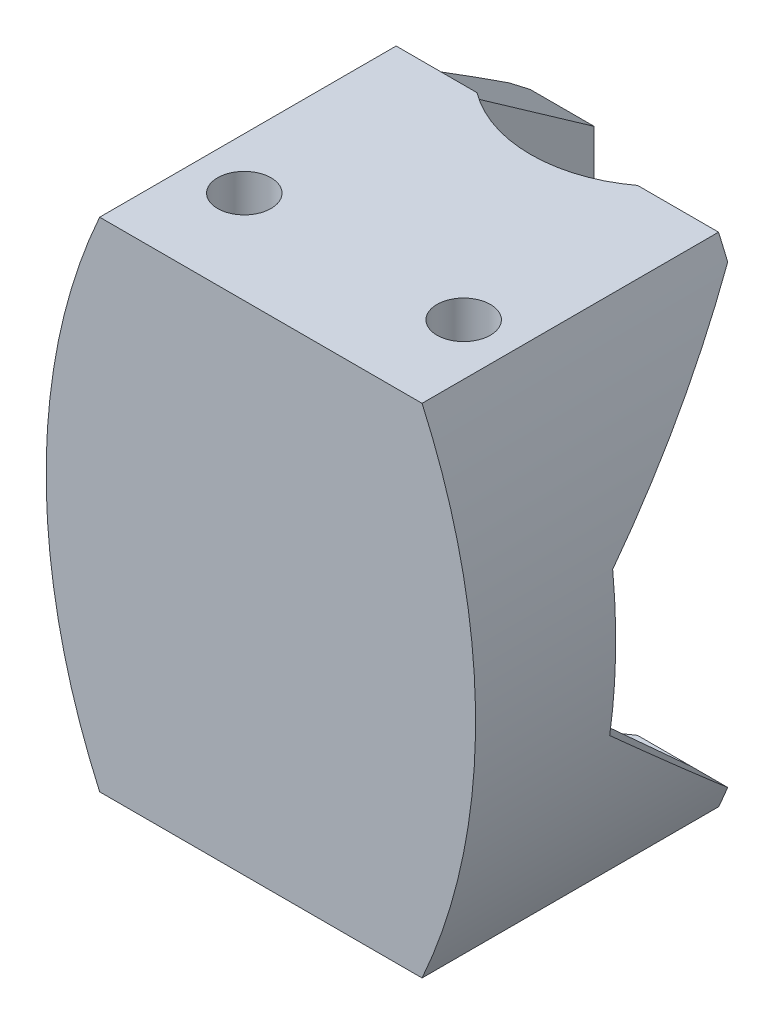
SolidWorks part; units mm, degrees
ref_plane "Front Plane" through (0, 0, 0) normal (0, 0, 1) x (1, 0, 0)
ref_plane "Top Plane" through (0, 0, 0) normal (0, 1, 0) x (1, 0, 0)
ref_plane "Right Plane" through (0, 0, 0) normal (1, 0, 0) x (0, 0, -1)
sketch "Sketch2" plane through (0, 0, 0) normal (0, 1, 0) x (1, 0, 0)
  line L0 (15.061, 0) -> (15.061, 37.7)
  line L1 (-12.561, 2.5) -> (12.561, 2.5)
  line L2 (-12.561, 2.5) -> (-12.561, 37.7)
  line L4 (12.561, 2.5) -> (12.561, 37.7)
  line L5 (15.061, 37.7) -> (12.561, 37.7)
  line L7 (-15.061, 37.7) -> (-15.061, 0)
  line L8 (-15.061, 0) -> (15.061, 0)
  line L10 (-15.061, 37.7) -> (-12.561, 37.7)
  point P4 (0, 2.5)
  point P12 (0, 0)
  dimension "D1" = 2.5
  dimension "D2" = 2.5
  dimension "D3" = 37.7
  dimension "D4" = 25.122
  dimension "D5" = 15.061
extrude "Boss-Extrude1" add sketch "Sketch2" along normal blind 32.5
sketch "Sketch4" plane through (0, 0, 0) normal (0, -1, 0) x (1, 0, 0)
  line L0 (-15.061, 0) -> (-15.061, -7.4438)
  line L8 (15.061, -7.4438) -> (15.061, 0)
  line L9 (15.061, 0) -> (-15.061, 0)
  line L10 (15.061, 0) -> (15.061, -37.7) construction
  line L13 (-15.061, -7.4438) -> (-15.061, -37.7)
  line L23 (-15.061, -37.7) -> (-12.561, -37.7)
  line L34 (-12.561, -37.7) -> (-12.561, -7.5)
  line L35 (-12.561, -2.5) -> (-12.561, -37.7) construction
  line L36 (-12.561, -7.5) -> (12.561, -7.5)
  line L37 (12.561, -37.7) -> (12.561, -2.5) construction
  line L38 (12.561, -7.5) -> (12.561, -37.7)
  line L39 (12.561, -37.7) -> (15.061, -37.7)
  line L40 (15.061, -37.7) -> (15.061, -7.4438)
  circle A2 centre (-10.2499, -4.95) radius 1.05
  circle A5 centre (10.2499, -4.95) radius 1.05
  dimension "D5" = 2.1
  dimension "D1" = 7.5
  dimension "D6" = 4.8111
  dimension "D7" = 4.95
  dimension "D8" = 4.8111
extrude "Boss-Extrude2" add sketch "Sketch4" along normal blind 2
sketch "Sketch7" plane through (0, -2, 0) normal (0, -1, 0) x (1, 0, 0)
  line L0 (-15.061, 0) -> (-15.061, -37.7)
  line L1 (-15.061, -37.7) -> (-12.561, -37.7)
  line L2 (-15.061, 0) -> (15.061, 0)
  line L4 (15.061, 0) -> (15.061, -37.7)
  line L5 (15.061, -37.7) -> (12.561, -37.7)
  line L6 (12.561, -37.7) -> (12.561, -7.5)
  line L7 (12.561, -7.5) -> (-12.561, -7.5)
  line L8 (-12.561, -7.5) -> (-12.561, -37.7)
  circle A2 centre (-10.2499, -4.95) radius 2.495
  circle A3 centre (10.2499, -4.95) radius 2.495
  dimension "D1" = 4.99
extrude "Wire spacing2" add sketch "Sketch7" along normal blind 3
sketch "Sketch8" plane through (0, -5, 0) normal (0, -1, 0) x (1, 0, 0)
  line L0 (-15.061, 0) -> (-15.061, -37.7)
  line L1 (-15.061, -37.7) -> (15.061, -37.7)
  line L2 (15.061, -37.7) -> (15.061, 0) construction
  line L3 (12.561, -37.7) -> (15.061, -37.7) construction
  line L4 (-15.061, 0) -> (15.061, 0)
  line L6 (15.061, 0) -> (15.061, -37.7)
  circle A0 centre (-10.2499, -4.95) radius 2.495
  circle A1 centre (10.2499, -4.95) radius 2.495
  circle A2 centre (10.2499, -4.95) radius 2.495 construction
  circle A3 centre (-10.2499, -4.95) radius 2.495 construction
extrude "Boss-Extrude6" add sketch "Sketch8" along normal blind 2
sketch "Sketch5" plane through (0, 32.5, 0) normal (0, 1, 0) x (1, 0, 0)
  line L0 (-7.5, 10) -> (-7.5, 2.5)
  line L9 (12.561, 2.5) -> (-12.561, 2.5) construction
  line L11 (-10.2499, 12) -> (-7.5, 10)
  line L13 (-15.061, 0) -> (15.061, 0) construction
  line L15 (-15.061, 0) -> (-15.061, 37.7)
  line L17 (10.2499, 12) -> (7.5, 10)
  line L20 (15.061, 0) -> (15.061, 37.7)
  line L21 (-7.5, 2.5) -> (7.5, 2.5)
  line L22 (7.5, 2.5) -> (7.5, 10)
  line L23 (-15.061, 0) -> (15.061, 0)
  line L24 (-10.2499, 12) -> (-12.561, 12)
  line L25 (-12.561, 37.7) -> (-12.561, 7.5) construction
  line L26 (-12.561, 12) -> (-12.561, 37.7)
  line L27 (-12.561, 37.7) -> (-15.061, 37.7)
  line L30 (15.061, 37.7) -> (12.561, 37.7)
  line L31 (12.561, 37.7) -> (12.561, 12)
  line L32 (12.561, 7.5) -> (12.561, 37.7) construction
  line L33 (12.561, 12) -> (10.2499, 12)
  circle A0 centre (-10.2499, 4.95) radius 1.05 construction
  circle A1 centre (-10.2499, 8.7) radius 1.05
  circle A2 centre (10.2499, 8.7) radius 1.05
  dimension "D4" = 0
  dimension "D7" = 8.7
  dimension "D1" = 12
  dimension "D2" = 7.561
  dimension "D3" = 20.4998
  dimension "D5" = 10
  dimension "D6" = 7.561
extrude "Boss-Extrude3" add sketch "Sketch5" along normal blind 2
sketch "Sketch9" plane through (0, 34.5, 0) normal (0, 1, 0) x (1, 0, 0)
  line L0 (-15.061, 0) -> (-15.061, 37.7)
  line L1 (-15.061, 37.7) -> (-12.561, 37.7)
  line L2 (-12.561, 37.7) -> (-12.561, 12)
  line L3 (-12.561, 12) -> (-10.2499, 12)
  line L4 (-10.2499, 12) -> (-7.5, 10)
  line L5 (-7.5, 10) -> (-7.5, 2.5)
  line L6 (-7.5, 2.5) -> (7.5, 2.5)
  line L7 (7.5, 2.5) -> (7.5, 10)
  line L8 (7.5, 10) -> (10.2499, 12)
  line L9 (10.2499, 12) -> (7.5, 10) construction
  line L10 (10.2499, 12) -> (12.561, 12)
  line L11 (12.561, 7.5) -> (12.561, 37.7) construction
  line L12 (12.561, 12) -> (12.561, 37.7)
  line L13 (12.561, 37.7) -> (15.061, 37.7)
  line L14 (15.061, 0) -> (15.061, 37.7) construction
  line L15 (15.061, 37.7) -> (12.561, 37.7) construction
  line L16 (15.061, 37.7) -> (15.061, 0)
  line L17 (15.061, 0) -> (-15.061, 0)
  circle A0 centre (-10.2499, 8.7) radius 2.495
  circle A1 centre (10.2499, 8.7) radius 2.495
  dimension "D1" = 4.99
extrude "Wire spacing1" add sketch "Sketch9" along normal blind 3
sketch "Sketch10" plane through (0, 37.5, 0) normal (0, 1, 0) x (1, 0, 0)
  line L1 (-15.061, 37.7) -> (15.061, 37.7)
  line L2 (-15.061, 37.7) -> (-15.061, 0)
  line L3 (-15.061, 0) -> (15.061, 0)
  line L4 (15.061, 37.7) -> (15.061, 0)
  circle A0 centre (-10.2499, 8.7) radius 2.495
  circle A1 centre (10.2499, 8.7) radius 2.495
  circle A2 centre (-10.2499, 8.7) radius 2.495 construction
  circle A3 centre (10.2499, 8.7) radius 2.495 construction
extrude "Boss-Extrude8" add sketch "Sketch10" along normal blind 2
sketch "Sketch11" plane through (0, 39.5, 0) normal (0, 1, 0) x (1, 0, 0)
  line L0 (15.061, 37.7) -> (-15.061, 37.7) construction
  circle A0 centre (0, 37.7) radius 12.5
  dimension "D1" = 25
extrude "Cut-Extrude1" cut sketch "Sketch11" against normal through all
ref_plane "Box Mid Plane" through (0, 16.25, 0) normal (0, 1, 0) x (1, 0, 0)
sketch "Sketch18" plane through (0, 39.5, 0) normal (0, 1, 0) x (1, 0, 0)
  line L1 (-15.061, 37.7) -> (-5.061, 37.7)
  line L2 (-15.061, 37.7) -> (-15.061, 27.7)
  line L3 (-15.061, 27.7) -> (-5.061, 27.7)
  line L4 (-5.061, 37.7) -> (-5.061, 27.7)
  line L5 (15.061, 37.7) -> (5.061, 37.7)
  line L6 (15.061, 37.7) -> (15.061, 27.7)
  line L7 (15.061, 27.7) -> (5.061, 27.7)
  line L8 (5.061, 37.7) -> (5.061, 27.7)
  dimension "D1" = 10
  dimension "D2" = 10
extrude "Cut-Extrude4" cut sketch "Sketch18" against normal through all
sketch "Sketch19" plane through (-15.061, 0, 0) normal (-1, 0, 0) x (0, 0, 1)
  line L0 (-27.7, 37.5) -> (-43.7, 26.25)
  line L1 (-43.7, 26.25) -> (-43.7, 6.25)
  line L2 (-43.7, 6.25) -> (-27.7, -5)
  line L3 (-27.7, -5) -> (-27.7, 37.5)
  point P3 (-27.7, 16.25)
  point P7 (-43.7, 16.25)
  dimension "D1" = 20
  dimension "D2" = 16
extrude "Boss-Extrude10" add sketch "Sketch19" against normal up to surface (2.5 mm away) up to face at (-12.561, 16.25, -12.425)
sketch "Sketch20" plane through (15.061, 0, 0) normal (1, 0, 0) x (0, 0, -1)
  line L0 (27.7, 37.5) -> (43.7, 26.25)
  line L1 (43.7, 26.25) -> (43.7, 6.25)
  line L2 (43.7, 6.25) -> (27.7, -5)
  line L3 (27.7, -5) -> (27.7, 37.5)
extrude "Boss-Extrude11" add sketch "Sketch20" against normal up to surface (2.5 mm away) up to face at (12.561, 16.25, -12.425)
sketch "Sketch21" plane through (0, 0, 0) normal (0, 0, 1) x (1, 0, 0)
  line L0 (15.061, 39.5) -> (15.061, -7)
  line L1 (-15.061, 39.5) -> (-15.061, -7)
  arc A1 (15.061, 39.5) -> (15.061, -7) centre (-36.4952, 16.25) cw
  arc A2 (-15.061, -7) -> (-15.061, 39.5) centre (36.4953, 16.25) cw
  point P10 (20.061, 16.25)
  point P11 (-20.061, 16.25)
  dimension "D1" = 5
  dimension "D2" = 5
extrude "Boss-Extrude12" add sketch "Sketch21" against normal up to surface (43.7 mm away) up to face at (13.811, 16.25, -43.7)
sketch "Sketch22" plane through (0, 0, 0) normal (1, 0, 0) x (0, 0, -1)
  line L0 (27.7, 37.5) -> (27.7, 39.5)
  line L1 (27.7, 39.5) -> (50.3727, 39.5)
  line L2 (50.3727, 39.5) -> (50.3727, -11.6168)
  line L3 (50.3727, -11.6168) -> (27.7, -11.6168)
  line L4 (27.7, -11.6168) -> (27.7, -5)
  line L5 (27.7, -5) -> (43.7, 6.25)
  line L6 (43.7, 6.25) -> (43.7, 26.25)
  line L7 (43.7, 26.25) -> (27.7, 37.5)
extrude "Cut-Extrude5" cut sketch "Sketch22" against normal through all both and the other way through all
sketch "Sketch23" plane through (12.561, 0, 0) normal (-1, 0, 0) x (0, 0, 1)
  line L0 (-27.7, 37.5) -> (-13.0912, 21.8818)
  line L1 (-13.0912, 21.8818) -> (-13.0912, 8.2927)
  line L2 (-13.0912, 8.2927) -> (-27.7, -5)
  line L3 (-27.7, -5) -> (-48.045, -3.3343)
  line L4 (-48.045, -3.3343) -> (-49.3531, 36.561)
  line L5 (-49.3531, 36.561) -> (-27.7, 37.5)
extrude "Cut-Extrude7" cut sketch "Sketch23" against normal through all
sketch "Sketch24" plane through (0, -7, 0) normal (0, -1, 0) x (1, 0, 0)
  line L1 (-19.53, -76.469) -> (19.53, -77.3247)
  line L2 (19.53, -77.3247) -> (19.53, -37.5)
  line L3 (-19.53, -37.5) -> (-36.2307, -37.5)
  line L4 (-36.2307, -37.5) -> (-36.2307, -76.469)
  line L5 (-36.2307, -76.469) -> (-19.53, -76.469)
  arc A0 (-19.53, -37.5) -> (19.53, -37.5) centre (0, -37.5) ccw
  dimension "D1" = 19.53
  dimension "D2" = 0
  dimension "D3" = 37.5
extrude "Cut-Extrude8" cut sketch "Sketch24" against normal through all
